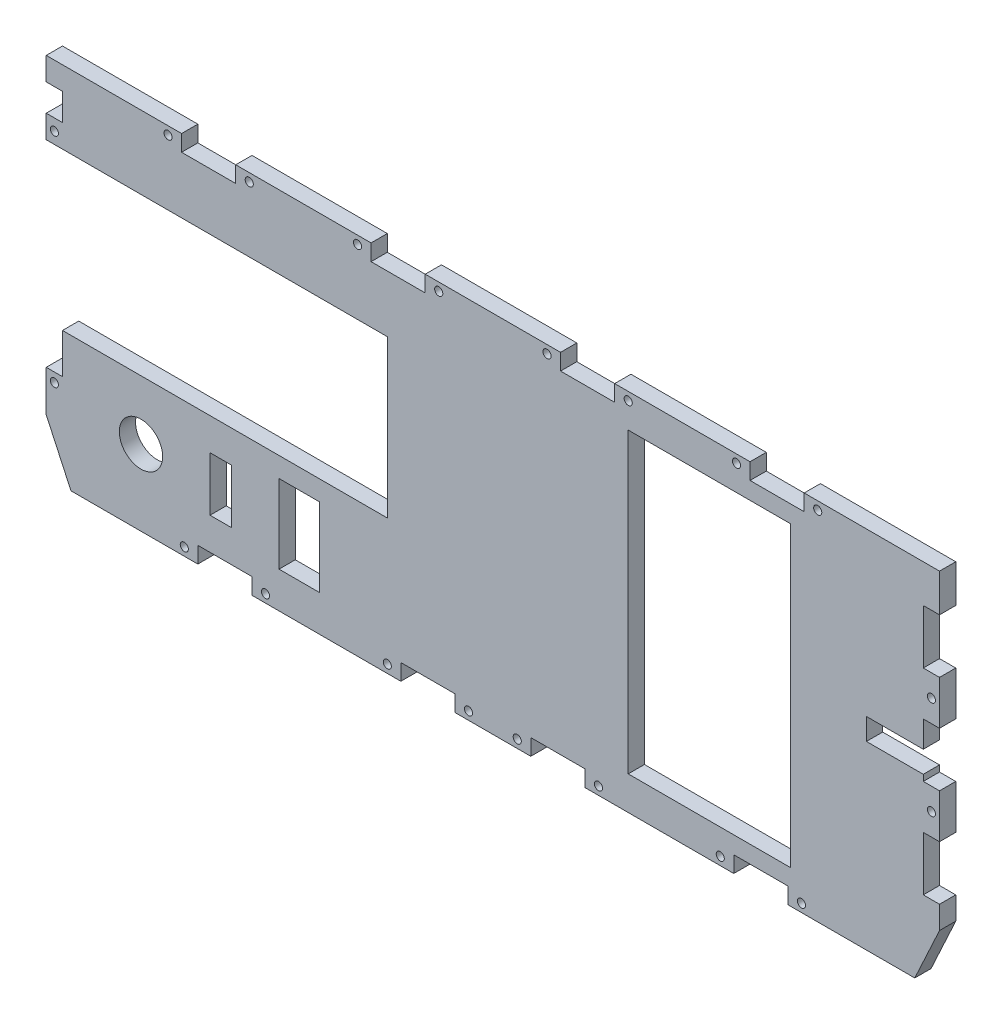
SolidWorks part; units mm, degrees
ref_plane "Plan de face" through (0, 0, 0) normal (0, 0, 1) x (1, 0, 0)
ref_plane "Plan de dessus" through (0, 0, 0) normal (0, 1, 0) x (1, 0, 0)
ref_plane "Plan de droite" through (0, 0, 0) normal (1, 0, 0) x (0, 0, -1)
sketch "Esquisse1" plane through (0, 0, 0) normal (0, 0, 1) x (1, 0, 0)
  line L0 (0, 124.9429) -> (0, -204.46) construction
  line L1 (-165, 96.73) -> (165, 96.73)
  line L2 (165, 96.73) -> (165, -18.27)
  line L3 (165, -18.27) -> (123, -109.0224)
  line L4 (123, -109.0224) -> (-123, -109.0224)
  line L5 (-211.9802, 0) -> (248.5953, 0) construction
  line L6 (-123, -109.0224) -> (-165, -18.27)
  line L7 (-165, -18.27) -> (-165, 96.73)
  dimension "D2" = 165
  dimension "D3" = 330
  dimension "D4" = 100
  dimension "D5" = 115
  dimension "D6" = 100
  dimension "D7" = 246
  dimension "D8" = 205.7524
  dimension "D9" = 96.73
  dimension "D10" = 115
extrude "Boss.-Extru.1" add sketch "Esquisse1" along normal blind 6
sketch "Esquisse3" plane through (0, 0, 0) normal (0, 0, -1) x (-1, 0, 0)
  line L0 (165, 96.73) -> (165, -18.27) construction
  line L1 (165, -3.06) -> (159, -3.06)
  line L2 (165, 69.73) -> (165, -3.06)
  line L3 (39, 11.73) -> (159, 11.73)
  line L4 (159, -3.06) -> (159, 11.73)
  line L5 (123, -109.0224) -> (-123, -109.0224) construction
  line L6 (165, 78.2326) -> (159, 78.2326)
  line L7 (165, 78.2326) -> (165, 88.2326)
  line L8 (165, 88.2326) -> (159, 88.2326)
  line L9 (159, 78.2326) -> (159, 88.2326)
  line L10 (-14, -38.02) -> (-14, -32.02)
  line L11 (109, -38.02) -> (89, -38.02)
  line L12 (109, -38.02) -> (109, -32.02)
  line L13 (109, -32.02) -> (89, -32.02)
  line L15 (0, -209.4812) -> (0, 177.1799) construction
  line L16 (-110, 84.355) -> (-50, 84.355)
  line L17 (-165, 82.73) -> (-159, 82.73)
  line L18 (89, -38.02) -> (89, -32.02)
  line L19 (34, -38.02) -> (14, -38.02)
  line L20 (34, -38.02) -> (34, -32.02)
  line L21 (34, -32.02) -> (14, -32.02)
  line L22 (-165, 82.73) -> (-165, 62.73)
  line L23 (-165, 62.73) -> (-159, 62.73)
  line L24 (-159, 82.73) -> (-159, 62.73)
  line L25 (-165, 46.44) -> (-159, 46.44)
  line L26 (-165, 46.44) -> (-165, 26.44)
  line L27 (-165, 26.44) -> (-159, 26.44)
  line L28 (-159, 46.44) -> (-159, 26.44)
  line L29 (-165, 10.15) -> (-159, 10.15)
  line L30 (-165, 96.73) -> (165, 96.73) construction
  line L31 (115, 96.73) -> (95, 96.73)
  line L32 (115, 96.73) -> (115, 90.73)
  line L33 (115, 90.73) -> (95, 90.73)
  line L34 (95, 96.73) -> (95, 90.73)
  line L35 (-25, 96.73) -> (-25, 90.73)
  line L36 (45, 96.73) -> (25, 96.73)
  line L37 (45, 96.73) -> (45, 90.73)
  line L38 (45, 90.73) -> (25, 90.73)
  line L39 (25, 96.73) -> (25, 90.73)
  line L40 (-45, 90.73) -> (-25, 90.73)
  line L41 (-45, 96.73) -> (-45, 90.73)
  line L42 (-45, 96.73) -> (-25, 96.73)
  line L43 (-95, 96.73) -> (-95, 90.73)
  line L44 (-115, 90.73) -> (-95, 90.73)
  line L45 (-115, 96.73) -> (-115, 90.73)
  line L46 (-115, 96.73) -> (-95, 96.73)
  line L47 (-165, 10.15) -> (-165, -9.85)
  line L48 (14, -38.02) -> (14, -32.02)
  line L49 (-34, -32.02) -> (-14, -32.02)
  line L50 (-34, -38.02) -> (-34, -32.02)
  line L51 (-34, -38.02) -> (-14, -38.02)
  line L52 (-165, -9.85) -> (-159, -9.85)
  line L53 (165, 69.73) -> (39, 69.73)
  line L54 (104.5, -20.145) -> (96.5, -20.145)
  line L55 (104.5, -20.145) -> (104.5, -0.145)
  line L56 (-159, 10.15) -> (-159, -9.85)
  line L57 (-89, -38.02) -> (-89, -32.02)
  line L58 (-109, -32.02) -> (-89, -32.02)
  line L59 (-109, -38.02) -> (-109, -32.02)
  line L60 (-109, -38.02) -> (-89, -38.02)
  line L61 (104.5, -0.145) -> (96.5, -0.145)
  line L62 (-110, 84.355) -> (-110, -25.645)
  line L63 (-110, -25.645) -> (-50, -25.645)
  line L64 (-50, 84.355) -> (-50, -25.645)
  line L65 (-165, -18.27) -> (-165, 96.73) construction
  line L66 (39, 69.73) -> (39, 11.73)
  line L67 (96.5, -20.145) -> (96.5, -0.145)
  line L68 (79, -24.645) -> (64, -24.645)
  line L69 (79, -24.645) -> (79, 4.355)
  line L70 (79, 4.355) -> (64, 4.355)
  line L71 (64, -24.645) -> (64, 4.355)
  circle A0 centre (130, -10.145) radius 8
  dimension "D44" = 16
  dimension "D45" = 21.875
  dimension "D42" = 35
  dimension "D47" = 17.5
  dimension "D2" = 6
  dimension "D3" = 6
  dimension "D4" = 10
  dimension "D5" = 6
  dimension "D6" = 20
  dimension "D7" = 60
  dimension "D8" = 55
  dimension "D9" = 8.4974
  dimension "D10" = 20
  dimension "D11" = 20
  dimension "D12" = 50
  dimension "D13" = 50
  dimension "D14" = 6
  dimension "D15" = 110
  dimension "D16" = 56
  dimension "D17" = 55
  dimension "D18" = 20
  dimension "D19" = 20
  dimension "D20" = 20
  dimension "D21" = 6
  dimension "D22" = 6
  dimension "D23" = 20
  dimension "D24" = 71.0024
  dimension "D25" = 71.0024
  dimension "D26" = 27
  dimension "D27" = 58
  dimension "D28" = 126
  dimension "D29" = 6.375
  dimension "D30" = 15.21
  dimension "D31" = 6
  dimension "D32" = 6
  dimension "D33" = 6
  dimension "D34" = 14
  dimension "D35" = 16.29
  dimension "D36" = 16.29
  dimension "D37" = 20
  dimension "D38" = 8
  dimension "D39" = 15
  dimension "D40" = 29
  dimension "D41" = 7.375
  dimension "D43" = 25
  dimension "D46" = 11.875
extrude "Enlèv. mat.-Extru.2" cut sketch "Esquisse3" against normal blind 6
sketch "Esquisse4" plane through (0, 0, 0) normal (0, 0, -1) x (-1, 0, 0)
  line L0 (159, 78.2326) -> (165, 78.2326) construction
  line L1 (115, 90.73) -> (115, 96.73) construction
  line L2 (120.102, -35.02) -> (4.7601, -35.02) construction
  line L3 (14, -32.02) -> (14, -38.02) construction
  line L4 (34, -38.02) -> (34, -32.02) construction
  line L5 (89, -32.02) -> (89, -38.02) construction
  line L6 (26.5287, 81.73) -> (-31.7243, 81.73) construction
  line L7 (109, -38.02) -> (109, -32.02) construction
  line L8 (165, 78.2326) -> (165, 69.73) construction
  line L9 (-120.102, -35.02) -> (-4.7601, -35.02) construction
  line L10 (-25, 96.73) -> (25, 96.73) construction
  line L11 (143.8632, 93.73) -> (-5, 93.73) construction
  line L12 (45, 96.73) -> (95, 96.73) construction
  line L13 (-162, -27.3544) -> (-162, 100.425) construction
  line L14 (95, 96.73) -> (95, 90.73) construction
  line L15 (45, 90.73) -> (45, 96.73) construction
  line L16 (25, 96.73) -> (25, 90.73) construction
  line L17 (0, 142.2997) -> (0, -202.2086) construction
  line L18 (-165, -18.27) -> (-165, -9.85) construction
  line L19 (-80, 84.355) -> (-80, -25.645) construction
  line L22 (162, -8.8216) -> (162, 103.5789) construction
  line L25 (-50, 84.355) -> (-110, 84.355) construction
  line L26 (-110, -25.645) -> (-50, -25.645) construction
  line L27 (-159, 46.44) -> (-165, 46.44) construction
  line L28 (-165, 26.44) -> (-159, 26.44) construction
  line L31 (159, -3.06) -> (165, -3.06) construction
  circle A1 centre (114, -35.02) radius 1.5
  circle A2 centre (162, 73.9826) radius 1.5
  circle A3 centre (84, -35.02) radius 1.5
  circle A4 centre (39, -35.02) radius 1.5
  circle A5 centre (162, -6.46) radius 1.5
  circle A6 centre (9, -35.02) radius 1.5
  circle A7 centre (-9, -35.02) radius 1.5
  circle A8 centre (-39, -35.02) radius 1.5
  circle A9 centre (-84, -35.02) radius 1.5
  circle A10 centre (120, 93.73) radius 1.5
  circle A11 centre (-114, -35.02) radius 1.5
  circle A12 centre (90, 93.73) radius 1.5
  circle A14 centre (50, 93.73) radius 1.5
  circle A15 centre (20, 93.73) radius 1.5
  circle A16 centre (-162, 18.29) radius 1.5
  circle A17 centre (-162, 54.585) radius 1.5
  circle A18 centre (-20, 93.73) radius 1.5
  circle A19 centre (-50, 93.73) radius 1.5
  circle A20 centre (-90, 93.73) radius 1.5
  circle A21 centre (-120, 93.73) radius 1.5
  dimension "D3" = 3
  dimension "D10" = 3
  dimension "D11" = 3
  dimension "D12" = 3
  dimension "D13" = 5
  dimension "D14" = 5
  dimension "D29" = 3
  dimension "D30" = 8.15
  dimension "D31" = 3
  dimension "D33" = 3
  dimension "D34" = 3
  dimension "D40" = 5
  dimension "D8" = 5
  dimension "D15" = 5
  dimension "D16" = 5
  dimension "D20" = 3.4
  dimension "D17" = 3
  dimension "D21" = 3
  dimension "D22" = 3
  dimension "D27" = 8.145
  dimension "D9" = 3
  dimension "D7" = 3
  dimension "D6" = 4.25
  dimension "D26" = 3
  dimension "D28" = 3
  dimension "D36" = 15
  dimension "D38" = 5
  dimension "D42" = 5
extrude "Enlèv. mat.-Extru.3" cut sketch "Esquisse4" against normal blind 6
sketch "Esquisse5" plane through (0, 0, 0) normal (0, 0, -1) x (-1, 0, 0)
  line L0 (45, 96.73) -> (95, 96.73) construction
  line L1 (209.7155, -38.02) -> (-246.3297, -38.02)
  line L2 (209.7155, -38.02) -> (209.7155, -174.249)
  line L3 (209.7155, -174.249) -> (-246.3297, -174.249)
  line L4 (-246.3297, -38.02) -> (-246.3297, -174.249)
  dimension "D1" = 134.75
extrude "Enlèv. mat.-Extru.4" cut sketch "Esquisse5" against normal blind 6
sketch "Esquisse6" plane through (0, 0, 0) normal (0, 0, -1) x (-1, 0, 0)
  line L0 (-159, 26.44) -> (-159, 46.44) construction
  line L1 (-159, 36.73) -> (-138, 36.73)
  line L2 (-159, 36.73) -> (-159, 28.73)
  line L3 (-159, 28.73) -> (-138, 28.73)
  line L4 (-138, 36.73) -> (-138, 28.73)
  line L5 (-165, 96.73) -> (-115, 96.73) construction
  dimension "D1" = 60
  dimension "D2" = 8
  dimension "D3" = 21
extrude "Enlèv. mat.-Extru.5" cut sketch "Esquisse6" against normal blind 10
